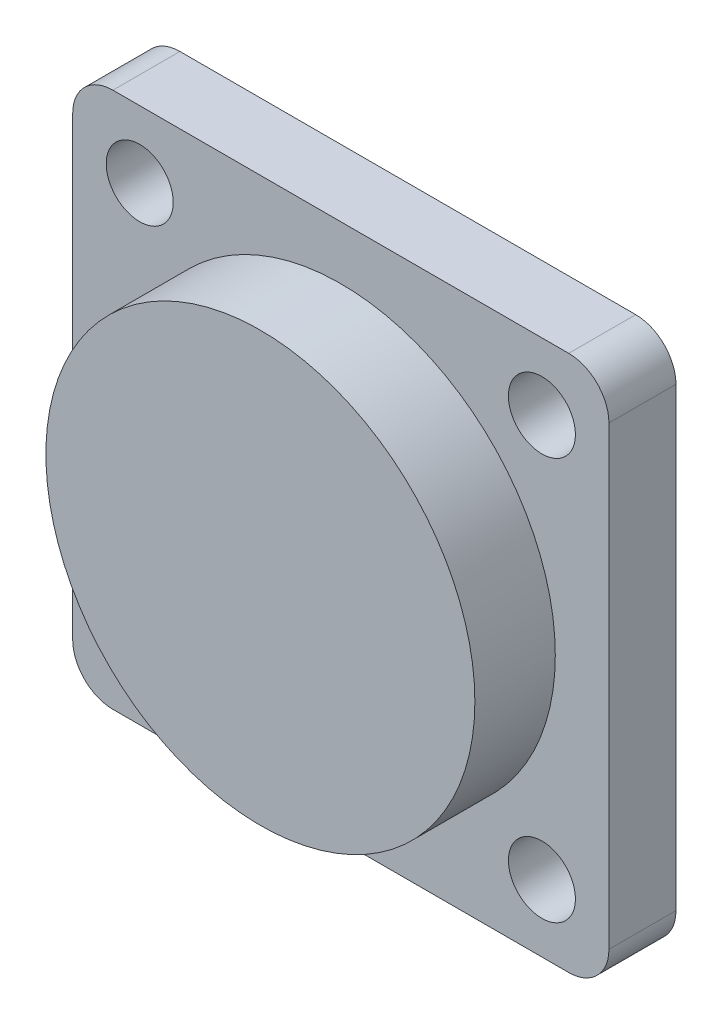
SolidWorks part; units mm, degrees
ref_plane "Front Plane" through (0, 0, 0) normal (0, 0, 1) x (1, 0, 0)
ref_plane "Top Plane" through (0, 0, 0) normal (0, 1, 0) x (1, 0, 0)
ref_plane "Right Plane" through (0, 0, 0) normal (1, 0, 0) x (0, 0, -1)
sketch "Sketch1" plane through (0, 0, 0) normal (0, 0, 1) x (1, 0, 0)
  line L1 (-20, 20) -> (20, 20)
  line L2 (-20, 20) -> (-20, -20)
  line L3 (-20, -20) -> (20, -20)
  line L4 (20, 20) -> (20, -20)
  line L5 (-20, 20) -> (20, -20) construction
  line L6 (-20, -20) -> (20, 20) construction
  line L7 (-15, 15) -> (15, 15) construction
  line L8 (-15, 15) -> (-15, -15) construction
  line L9 (-15, -15) -> (15, -15) construction
  line L10 (15, 15) -> (15, -15) construction
  line L11 (-15, 15) -> (15, -15) construction
  line L12 (-15, -15) -> (15, 15) construction
  circle A0 centre (-15, 15) radius 2.5
  circle A1 centre (15, 15) radius 2.5
  circle A2 centre (15, -15) radius 2.5
  circle A3 centre (-15, -15) radius 2.5
  point P0 (0, 0)
  point P6 (0, 0)
  dimension "D4" = 5
  dimension "D1" = 5
  dimension "D2" = 40
  dimension "D3" = 40
extrude "Boss-Extrude1" add sketch "Sketch1" along normal blind 5
sketch "Sketch2" plane through (0, 0, 5) normal (0, 0, 1) x (1, 0, 0)
  circle A0 centre (0, 0) radius 16
  dimension "D1" = 32
extrude "Boss-Extrude2" add sketch "Sketch2" along normal blind 6
fillet "Fillet2" radius 3 4 edges at (-20, -20, 2.5) (20, -20, 2.5) (20, 20, 2.5) (-20, 20, 2.5)
